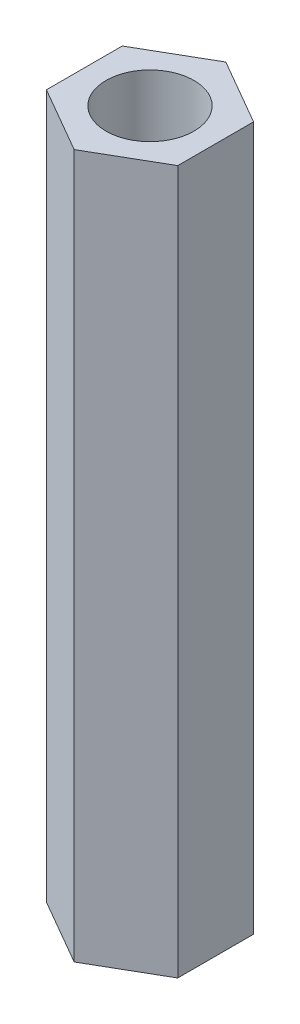
SolidWorks part; units mm, degrees
ref_plane "Front Plane" through (0, 0, 0) normal (0, 0, 1) x (1, 0, 0)
ref_plane "Top Plane" through (0, 0, 0) normal (0, 1, 0) x (1, 0, 0)
ref_plane "Right Plane" through (0, 0, 0) normal (1, 0, 0) x (0, 0, -1)
sketch "Sketch1" plane through (0, 0, 0) normal (0, 1, 0) x (1, 0, 0)
  line L1 (0, -2.0531) -> (1.778, -1.0265)
  line L2 (1.778, -1.0265) -> (1.778, 1.0265)
  line L3 (1.778, 1.0265) -> (0, 2.0531)
  line L4 (0, 2.0531) -> (-1.778, 1.0265)
  line L5 (-1.778, 1.0265) -> (-1.778, -1.0265)
  line L6 (-1.778, -1.0265) -> (0, -2.0531)
  circle A0 centre (0, 0) radius 1.778 construction
  circle A1 centre (0, 0) radius 1.1906
  dimension "D1" = 2.3813
  dimension "D2" = 1.778
extrude "Boss-Extrude1" add sketch "Sketch1" along normal blind 19.05
